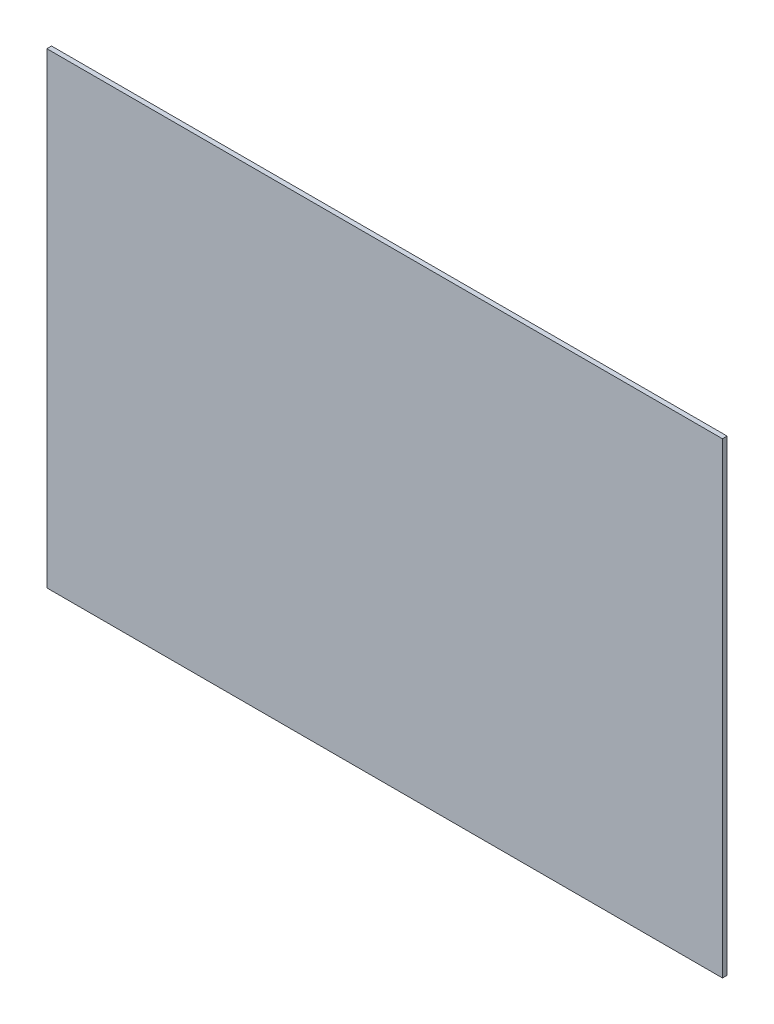
SolidWorks part; units mm, degrees
ref_plane "Plan de face" through (0, 0, 0) normal (0, 0, 1) x (1, 0, 0)
ref_plane "Plan de dessus" through (0, 0, 0) normal (0, 1, 0) x (1, 0, 0)
ref_plane "Plan de droite" through (0, 0, 0) normal (1, 0, 0) x (0, 0, -1)
sketch "Esquisse1" plane through (0, 0, 0) normal (0, 0, 1) x (1, 0, 0)
  line L1 (-217, 150) -> (217, 150)
  line L2 (-217, 150) -> (-217, -150)
  line L3 (-217, -150) -> (217, -150)
  line L4 (217, 150) -> (217, -150)
  line L5 (-217, 150) -> (217, -150) construction
  line L6 (-217, -150) -> (217, 150) construction
  point P0 (0, 0)
  dimension "D1" = 434
  dimension "D2" = 300
extrude "Boss.-Extru.1" add sketch "Esquisse1" along normal blind 3
